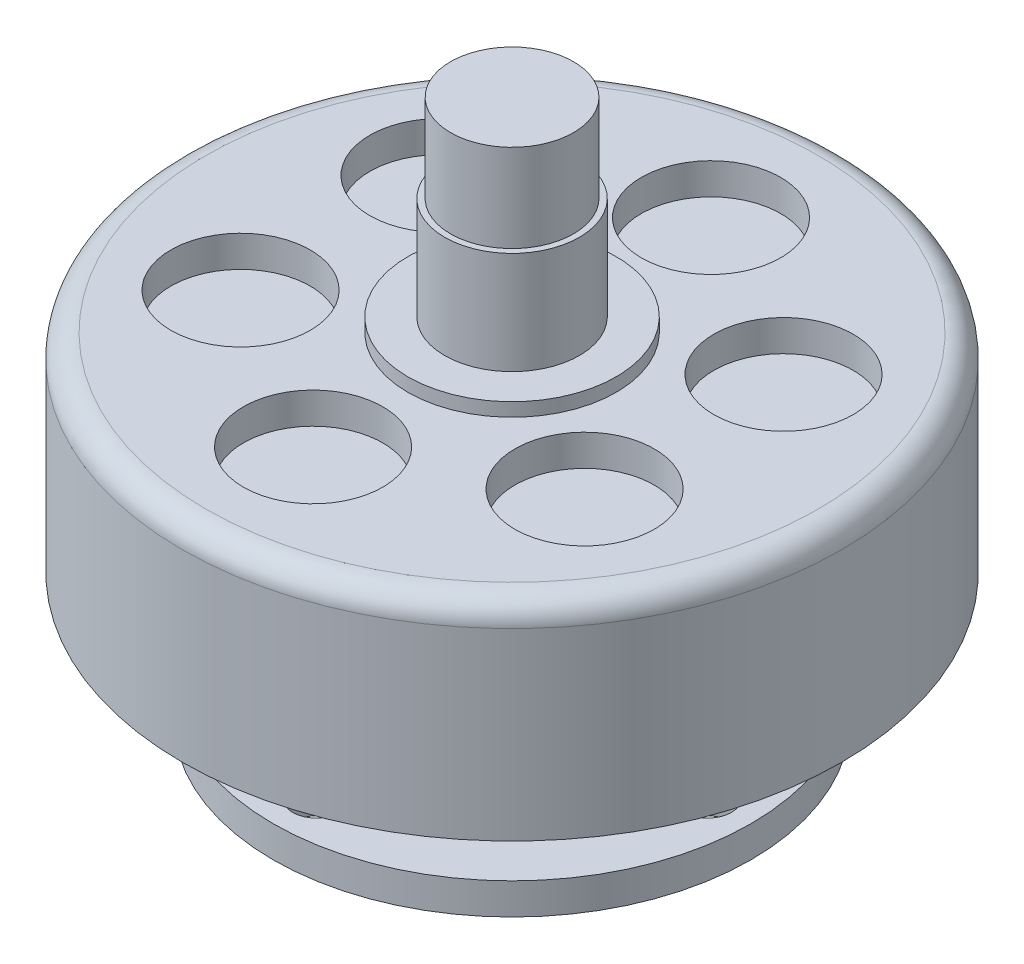
SolidWorks part; units mm, degrees
material "6061-T6 (SS)"
ref_plane "Alzado" through (0, 0, 0) normal (0, 0, 1) x (1, 0, 0)
ref_plane "Planta" through (0, 0, 0) normal (0, 1, 0) x (1, 0, 0)
ref_plane "Vista lateral" through (0, 0, 0) normal (1, 0, 0) x (0, 0, -1)
sketch "Croquis1" plane through (0, 0, 0) normal (0, 1, 0) x (1, 0, 0)
  circle A0 centre (0, 0) radius 21.05
  dimension "D1" = 42.1
extrude "Saliente-Extruir1" add sketch "Croquis1" along normal blind 13.25
fillet "Redondeo1" radius 1.5 1 edges at (0, 13.25, 21.05)
sketch "Croquis2" plane through (0, 13.25, 0) normal (0, 1, 0) x (1, 0, 0)
  circle A0 centre (0.011, 12.6912) radius 4.45
  circle A1 centre (10.9964, 6.3361) radius 4.45
  circle A2 centre (10.9854, -6.3551) radius 4.45
  circle A3 centre (-0.011, -12.6912) radius 4.45
  circle A4 centre (-10.9964, -6.3361) radius 4.45
  circle A5 centre (-10.9854, 6.3551) radius 4.45
  point P15 (0, 0)
  dimension "D2" = 8.9
  dimension "D1" = 6
extrude "Cortar-Extruir1" cut sketch "Croquis2" against normal blind 2
sketch "Croquis3" plane through (0, 13.25, 0) normal (0, 1, 0) x (1, 0, 0)
  circle A0 centre (0, 0) radius 3.925
  dimension "D1" = 7.85
extrude "Saliente-Extruir2" add sketch "Croquis3" along normal blind 13
sketch "Croquis4" plane through (0, 0, 0) normal (0, -1, 0) x (1, 0, 0)
  circle A0 centre (0, 0) radius 5.9087
extrude "Saliente-Extruir3" add sketch "Croquis4" along normal blind 6.3
sketch "Croquis5" plane through (0, -6.3, 0) normal (0, -1, 0) x (1, 0, 0)
  circle A0 centre (0, 0) radius 15.25
  circle A1 centre (0, 12.5) radius 1.5
  circle A2 centre (12.5, 0) radius 1.5
  circle A3 centre (0, -12.5) radius 1.5
  circle A4 centre (-12.5, 0) radius 1.5
  point P14 (0, 0)
  dimension "D2" = 3
  dimension "D3" = 25
  dimension "D4" = 30.5
  dimension "D1" = 4
extrude "Saliente-Extruir4" add sketch "Croquis5" along normal blind 2
sketch "Croquis6" plane through (0, -8.3, 0) normal (0, -1, 0) x (1, 0, 0)
  circle A0 centre (0, 0) radius 2
  dimension "D1" = 4
extrude "Saliente-Extruir5" add sketch "Croquis6" along normal blind 2.7
sketch "Croquis7" plane through (0, -8.3, 0) normal (0, -1, 0) x (1, 0, 0)
  circle A0 centre (0, 0) radius 3
  dimension "D1" = 6
extrude "Saliente-Extruir6" add sketch "Croquis7" along normal blind 1.2
sketch "Croquis8" plane through (0, -9.5, 0) normal (0, -1, 0) x (1, 0, 0)
  line L0 (-1.75, 0.0105) -> (-1.75, 3.45)
  line L1 (-1.75, 3.45) -> (1.75, 3.45)
  line L2 (1.75, 3.45) -> (1.75, 0.0105)
  line L3 (1.75, 0.0105) -> (-1.75, 0.0105)
  circle A0 centre (0, 0) radius 2 construction
  point P4 (0, 3.45)
  dimension "D1" = 3.5
  dimension "D2" = 3.45
extrude "Saliente-Extruir7" add sketch "Croquis8" along normal blind 0.2
sketch "Croquis9" plane through (0, 13.25, 0) normal (0, 1, 0) x (1, 0, 0)
  circle A0 centre (0, 0) radius 4.3
  dimension "D1" = 8.6
extrude "Saliente-Extruir8" add sketch "Croquis9" along normal blind 7.4
sketch "Croquis10" plane through (0, 13.25, 0) normal (0, 1, 0) x (1, 0, 0)
  circle A0 centre (0, 0) radius 6.65
  dimension "D1" = 13.3
extrude "Saliente-Extruir9" add sketch "Croquis10" along normal blind 0.86
